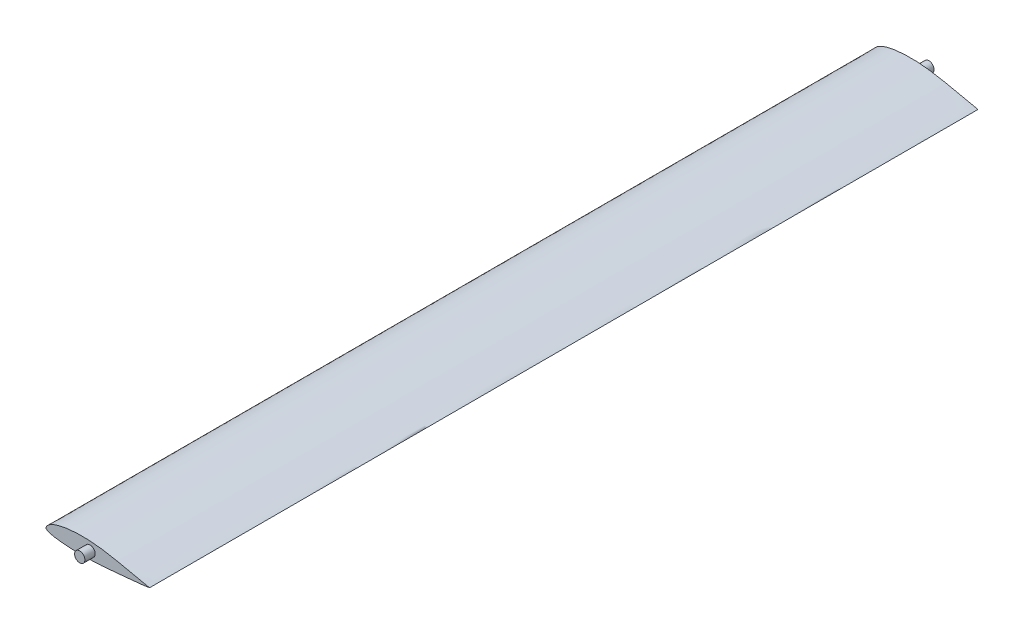
SolidWorks part; units mm, degrees
ref_plane "Front Plane" through (0, 0, 0) normal (0, 0, 1) x (1, 0, 0)
ref_plane "Top Plane" through (0, 0, 0) normal (0, 1, 0) x (1, 0, 0)
ref_plane "Right Plane" through (0, 0, 0) normal (1, 0, 0) x (0, 0, -1)
other "Center of Mass"
curve "Curve1"
  spline degree 3 poles (2527.2785, -0.7303, 0) (2543.335, -0.1392, 0) (2527.3878, 1.7851, 0) (2515.5292, 5.8817, 0) (2488.2293, 12.9019, 0) (2456.0322, 21.5149, 0) (2414.6563, 30.5876, 0) (2365.9234, 40.6704, 0) (2309.555, 52.1365, 0) (2246.3285, 65.0018, 0) (2176.8454, 79.2335, 0) (2101.848, 94.6989, 0) (2022.0633, 111.2691, 0) (1938.2558, 128.7364, 0) (1851.199, 146.8068, 0) (1761.6772, 165.1783, 0) (1670.4955, 183.4458, 0) (1578.3561, 201.2005, 0) (1485.682, 217.4895, 0) (1392.8204, 231.8087, 0) (1300.1686, 244.3615, 0) (1207.9719, 254.5594, 0) (1116.615, 262.183, 0) (1026.4456, 267.4992, 0) (937.7782, 270.0921, 0) (850.9529, 270.2351, 0) (766.3332, 267.999, 0) (684.3606, 263.32, 0) (605.4281, 256.5267, 0) (529.9495, 247.6046, 0) (458.3473, 236.734, 0) (390.9977, 223.9986, 0) (328.257, 209.4348, 0) (270.4064, 193.2972, 0) (217.6983, 175.6631, 0) (170.4327, 156.5598, 0) (128.6047, 136.5626, 0) (92.5134, 115.5502, 0) (62.2563, 94.0194, 0) (37.7679, 72.3218, 0) (19.4549, 50.4341, 0) (6.8635, 29.1069, 0) (0.0718, 9.6345, 0) (-1.2744, -9.2497, 0) (10.506, -25.1906, 0) (29.9207, -37.7525, 0) (56.6108, -50.6963, 0) (90.7122, -62.9707, 0) (132.0134, -74.4238, 0) (180.2672, -85.0557, 0) (235.1786, -94.9227, 0) (296.4203, -103.7415, 0) (363.5588, -111.7313, 0) (436.1664, -118.7122, 0) (513.7173, -124.7171, 0) (595.729, -129.6182, 0) (681.6869, -133.281, 0) (771.0708, -135.7351, 0) (863.36, -136.8526, 0) (958.0353, -136.4946, 0) (1054.5924, -134.8917, 0) (1152.5523, -131.7102, 0) (1251.3817, -127.126, 0) (1350.6396, -121.2679, 0) (1449.8899, -113.972, 0) (1548.7058, -105.6527, 0) (1646.5442, -96.8886, 0) (1742.6645, -87.746, 0) (1836.3702, -78.5986, 0) (1926.9226, -69.5519, 0) (2013.6035, -60.8665, 0) (2095.6864, -52.6026, 0) (2172.4693, -44.8786, 0) (2243.2725, -37.7621, 0) (2307.4392, -31.3213, 0) (2364.4156, -25.3996, 0) (2413.512, -19.9897, 0) (2455.1291, -14.6994, 0) (2487.6157, -8.8211, 0) (2515.1953, -4.0042, 0) (2527.2785, -0.7303, 0) (2543.335, -0.1392, 0) (2527.3878, 1.7851, 0) knots -0.00957 -0.004539 -0.001196 0 0.001194 0.00454 0.009601 0.016135 0.024161 0.033728 0.044763 0.057157 0.070769 0.085471 0.10111 0.11754 0.134608 0.152144 0.169995 0.187984 0.206002 0.224 0.241912 0.259664 0.277235 0.294525 0.311503 0.328142 0.344355 0.360082 0.375262 0.389821 0.403699 0.416824 0.429154 0.440657 0.451284 0.461038 0.469901 0.477873 0.484977 0.491187 0.496596 0.501303 0.50529 0.508453 0.511643 0.51604 0.521704 0.528625 0.536817 0.546289 0.556976 0.568832 0.581797 0.595781 0.610696 0.626441 0.642935 0.660077 0.677763 0.695909 0.714417 0.73319 0.752163 0.771203 0.790259 0.809283 0.828121 0.846641 0.864703 0.882162 0.898875 0.914705 0.929514 0.94317 0.955547 0.966536 0.976028 0.983961 0.99043 0.995461 0.998804 1 1.001194 1.00454 1.009601 periodic
sketch "Sketch1" plane through (0, 0, 0) normal (0, 0, 1) x (1, 0, 0)
  line L0 (0, 0) -> (0, 7.9474) construction
  line L1 (0, 0) -> (50, 0) construction
  spline S1 degree 3 poles (49.7496, -0.0143) (50.0656, -0.0028) (49.7518, 0.0352) (49.5184, 0.116) (48.9811, 0.2544) (48.3475, 0.4242) (47.5332, 0.6031) (46.5741, 0.8019) (45.4647, 1.0281) (44.2204, 1.2818) (42.8529, 1.5625) (41.3769, 1.8675) (39.8067, 2.1943) (38.1573, 2.5388) (36.4439, 2.8951) (34.6821, 3.2575) (32.8876, 3.6178) (31.0742, 3.968) (29.2503, 4.2893) (27.4226, 4.5719) (25.5991, 4.8198) (23.7846, 5.0212) (21.9865, 5.172) (20.2118, 5.2774) (18.4666, 5.3292) (16.7577, 5.3327) (15.0921, 5.2894) (13.4787, 5.198) (11.9251, 5.0649) (10.4394, 4.8899) (9.03, 4.6765) (7.7043, 4.4264) (6.4693, 4.1403) (5.3305, 3.8231) (4.2929, 3.4765) (3.3625, 3.1009) (2.539, 2.7076) (1.8285, 2.2943) (1.2328, 1.8708) (0.7506, 1.4439) (0.39, 1.0133) (0.142, 0.5936) (0.0082, 0.2104) (-0.0185, -0.1613) (0.2132, -0.4751) (0.5953, -0.7225) (1.1205, -0.9775) (1.7916, -1.2194) (2.6044, -1.4451) (3.5541, -1.6548) (4.6348, -1.8495) (5.8401, -2.0235) (7.1615, -2.1813) (8.5905, -2.3193) (10.1168, -2.4382) (11.731, -2.5353) (13.4228, -2.6081) (15.1821, -2.6571) (16.9986, -2.6799) (18.862, -2.6736) (20.7625, -2.6428) (22.6906, -2.581) (24.6358, -2.4916) (26.5895, -2.3771) (28.5431, -2.2343) (30.4881, -2.0714) (32.4138, -1.8997) (34.3058, -1.7205) (36.1502, -1.5413) (37.9326, -1.3639) (39.6387, -1.1937) (41.2544, -1.0317) (42.7657, -0.8803) (44.1594, -0.7408) (45.4224, -0.6146) (46.5439, -0.4985) (47.5102, -0.3924) (48.3294, -0.2886) (48.9689, -0.1732) (49.5118, -0.0786) (49.7496, -0.0143) (50.0656, -0.0028) (49.7518, 0.0352) knots -0.00957 -0.004539 -0.001196 0 0.001194 0.00454 0.009601 0.016135 0.024161 0.033728 0.044763 0.057157 0.070769 0.085471 0.10111 0.11754 0.134608 0.152144 0.169995 0.187984 0.206002 0.224 0.241912 0.259664 0.277235 0.294525 0.311503 0.328142 0.344355 0.360082 0.375262 0.389821 0.403699 0.416824 0.429154 0.440657 0.451284 0.461038 0.469901 0.477873 0.484977 0.491187 0.496596 0.501303 0.50529 0.508453 0.511643 0.51604 0.521704 0.528625 0.536817 0.546289 0.556976 0.568832 0.581797 0.595781 0.610696 0.626441 0.642935 0.660077 0.677763 0.695909 0.714417 0.73319 0.752163 0.771203 0.790259 0.809283 0.828121 0.846641 0.864703 0.882162 0.898875 0.914705 0.929514 0.94317 0.955547 0.966536 0.976028 0.983961 0.99043 0.995461 0.998804 1 1.001194 1.00454 1.009601 only from (50, 0) to (50, 0)
  dimension "D1" = 50
extrude "Boss-Extrude1" add sketch "Sketch1" along normal mid plane 400 contours S1
other "Center of Mass Reference Point1"
sketch "Sketch3" plane through (0, 0, 0) normal (0, 0, 1) x (1, 0, 0)
  circle A0 centre (21.2826, 1.0439) radius 2.5
  dimension "D1" = 5
  dimension "D2" = 0
  dimension "D3" = 0
extrude "Boss-Extrude2" add sketch "Sketch3" along normal blind 5 from surface at 200
mirror "Mirror1" about plane through (0, 0, 0) normal (0, 0, 1) of "Boss-Extrude2"
